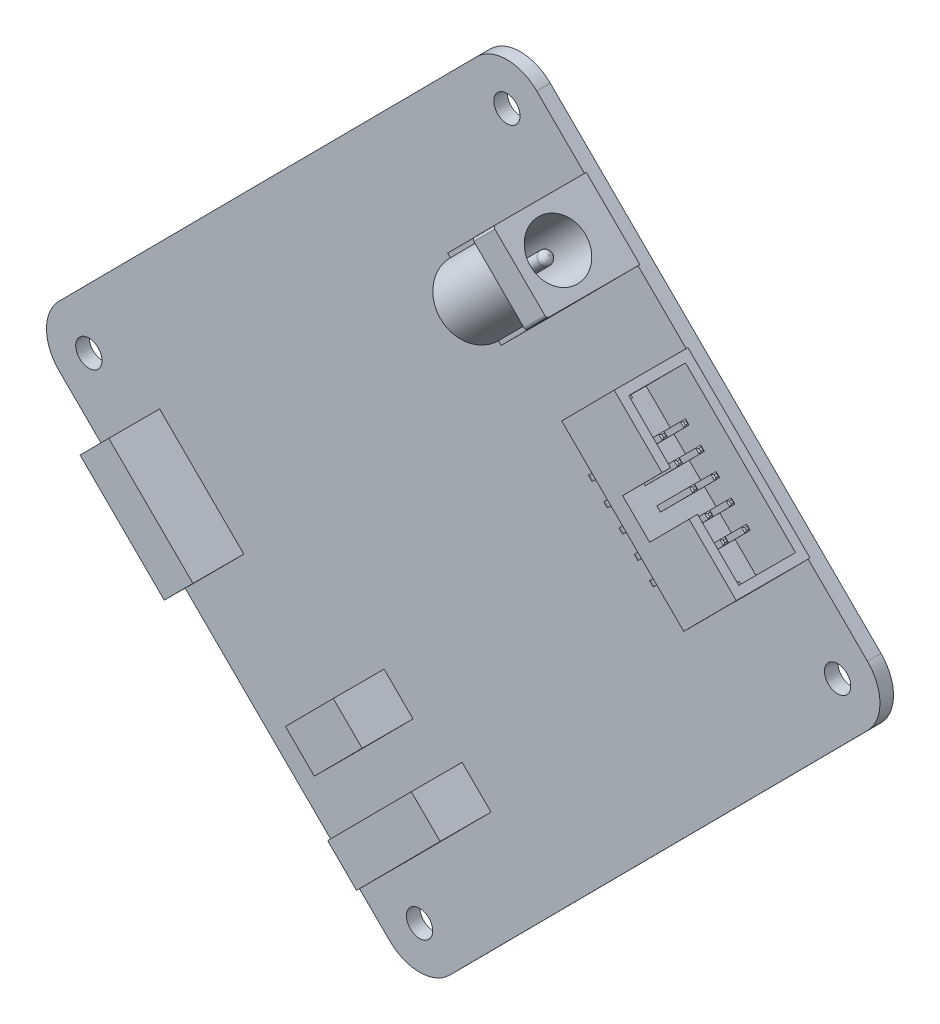
SolidWorks part; units mm, degrees
ref_plane "Front" through (0, 0, 0) normal (0, 0, 1) x (1, 0, 0)
ref_plane "Top" through (0, 0, 0) normal (0, 1, 0) x (1, 0, 0)
ref_plane "Right" through (0, 0, 0) normal (1, 0, 0) x (0, 0, -1)
sketch "草图1" plane through (0, 0, 0) normal (0, 0, 1) x (1, 0, 0)
  line L0 (-46.2191, -2.6231) -> (3.1095, 47.0427)
  line L1 (10.1805, 47.0668) -> (49.2036, 8.3086)
  line L2 (49.2277, 1.2376) -> (-0.1009, -48.4282)
  line L3 (-7.1719, -48.4523) -> (-46.195, -9.6941)
  arc A0 (-0.1009, -48.4282) -> (-7.1719, -48.4523) centre (-3.6484, -44.9047) cw
  arc A1 (49.2036, 8.3086) -> (49.2277, 1.2376) centre (45.6801, 4.761) cw
  arc A2 (3.1095, 47.0427) -> (10.1805, 47.0668) centre (6.657, 43.5192) cw
  arc A3 (-46.2191, -2.6231) -> (-46.195, -9.6941) centre (-42.6716, -6.1466) ccw
  point P6 (-3.6244, -51.9758)
  point P9 (52.7512, 4.7851)
  point P12 (6.6329, 50.5903)
  dimension "D3" = 5
  dimension "D1" = 65
  dimension "D2" = 80
extrude "凸台-拉伸1" add sketch "草图1" along normal blind 1.6
sketch "草图2" plane through (0, 0, 1.6) normal (0, 0, 1) x (1, 0, 0)
  circle A0 centre (6.657, 43.5192) radius 1.55
  circle A1 centre (-42.6716, -6.1466) radius 1.55
  circle A2 centre (-3.6484, -44.9047) radius 1.55
  circle A3 centre (45.6801, 4.761) radius 1.55
  dimension "D1" = 3.1
  dimension "D2" = 3.1
  dimension "D3" = 3.1
  dimension "D4" = 3.1
extrude "切除-拉伸1" cut sketch "草图2" against normal blind 1.6
sketch "草图3" plane through (0, 0, 1.6) normal (0, 0, 1) x (1, 0, 0)
  line L0 (28.0233, 29.768) -> (21.822, 23.5243)
  line L2 (21.822, 23.5243) -> (36.225, 9.219)
  line L3 (36.225, 9.219) -> (42.4263, 15.4627)
  line L4 (42.4263, 15.4627) -> (28.0233, 29.768)
  line L5 (35.2248, 22.6153) -> (29.0235, 16.3716) construction
  line L6 (3.1095, 47.0427) -> (-46.2191, -2.6231) construction
  line L7 (49.2036, 8.3086) -> (10.1805, 47.0668) construction
  dimension "D1" = 8.8
  dimension "D2" = 40
  dimension "D3" = 10.15
  dimension "D4" = 8.5
extrude "凸台-拉伸2" add sketch "草图3" along normal blind 8.7
sketch "草图4" plane through (28.7998, 28.9967, 0) normal (0.7047, 0.7095, 0) x (0.7095, -0.7047, 0)
  line L0 (18.2055, -9.3) -> (11.3555, -9.3)
  line L1 (11.3555, -9.3) -> (11.3555, -10.3)
  line L2 (19.2055, -10.3) -> (-1.0945, -10.3) construction
  line L3 (11.3555, -10.3) -> (6.8555, -10.3)
  line L4 (6.8555, -10.3) -> (6.8555, -9.3)
  line L5 (6.8555, -9.3) -> (-0.0945, -9.3)
  line L6 (-0.0945, -9.3) -> (-0.0945, -2.6)
  line L7 (-0.0945, -2.6) -> (18.2055, -2.6)
  line L8 (18.2055, -2.6) -> (18.2055, -9.3)
  line L9 (-1.0945, -10.3) -> (-1.0945, -1.6) construction
  line L10 (19.2055, -10.3) -> (19.2055, -1.6) construction
  line L11 (29.0555, -1.6) -> (19.2055, -1.6) construction
  dimension "D1" = 1
  dimension "D2" = 1
  dimension "D3" = 1
  dimension "D4" = 1
  dimension "D5" = 1
  dimension "D6" = 4.5
  dimension "D7" = 7.85
extrude "切除-拉伸2" cut sketch "草图4" against normal offset from surface (6.6 mm away) 2.2 up to face at (29.0235, 16.3716, 5.95)
sketch "草图5" plane through (13.6265, -13.534, 0) normal (0.7095, -0.7047, 0) x (0, 0, -1)
  line L0 (-7.8, 32.0686) -> (-7.8, 38.5686)
  line L1 (-10.3, 32.0686) -> (-1.6, 32.0686) construction
  line L2 (-7.8, 38.5686) -> (-4.4, 38.5686)
  line L3 (-4.4, 38.5686) -> (-4.4, 32.0686)
  line L4 (-4.4, 32.0686) -> (-7.8, 32.0686)
  line L5 (-10.3, 32.0686) -> (-10.3, 40.8686) construction
  dimension "D1" = 3.4
  dimension "D2" = 6.5
  dimension "D3" = 2.5
extrude "切除-拉伸3" cut sketch "草图5" against normal blind 1.3
sketch "草图6" plane through (-0.7766, 0.7713, 0) normal (-0.7095, 0.7047, 0) x (0, 0, 1)
  line L0 (10.3, 32.0686) -> (1.6, 32.0686) construction
  line L1 (7.8, 32.0686) -> (4.4, 32.0686)
  line L2 (7.8, 32.0686) -> (7.8, 38.5686)
  line L3 (7.8, 38.5686) -> (4.4, 38.5686)
  line L4 (4.4, 32.0686) -> (4.4, 38.5686)
  line L5 (10.3, 40.8686) -> (10.3, 32.0686) construction
  dimension "D1" = 3.4
  dimension "D2" = 6.5
  dimension "D3" = 2.5
extrude "切除-拉伸4" cut sketch "草图6" against normal blind 1.3
sketch "草图7" plane through (24.1488, 24.3139, 0) normal (0.7047, 0.7095, 0) x (0.7095, -0.7047, 0)
  line L0 (11.3555, -9.3) -> (18.2055, -9.3) construction
  line L1 (14.7055, -7.8) -> (14.1055, -7.8)
  line L2 (14.7055, -7.8) -> (14.7055, -7.2)
  line L3 (14.7055, -7.2) -> (14.1055, -7.2)
  line L4 (14.1055, -7.8) -> (14.1055, -7.2)
  line L5 (18.2055, -9.3) -> (18.2055, -2.6) construction
  line L6 (12.1655, -7.8) -> (12.1655, -7.2)
  line L7 (12.1655, -7.8) -> (11.5655, -7.8)
  line L8 (11.5655, -7.8) -> (11.5655, -7.2)
  line L9 (12.1655, -7.2) -> (11.5655, -7.2)
  line L10 (9.6255, -7.8) -> (9.6255, -7.2)
  line L11 (9.6255, -7.8) -> (9.0255, -7.8)
  line L12 (9.0255, -7.8) -> (9.0255, -7.2)
  line L13 (9.6255, -7.2) -> (9.0255, -7.2)
  line L14 (7.0855, -7.8) -> (7.0855, -7.2)
  line L15 (7.0855, -7.8) -> (6.4855, -7.8)
  line L16 (6.4855, -7.8) -> (6.4855, -7.2)
  line L17 (7.0855, -7.2) -> (6.4855, -7.2)
  line L18 (4.5455, -7.8) -> (4.5455, -7.2)
  line L19 (4.5455, -7.8) -> (3.9455, -7.8)
  line L20 (3.9455, -7.8) -> (3.9455, -7.2)
  line L21 (4.5455, -7.2) -> (3.9455, -7.2)
  line L22 (12.1655, -5.26) -> (12.1655, -4.66)
  line L23 (12.1655, -5.26) -> (11.5655, -5.26)
  line L24 (11.5655, -5.26) -> (11.5655, -4.66)
  line L25 (12.1655, -4.66) -> (11.5655, -4.66)
  line L26 (9.6255, -5.26) -> (9.6255, -4.66)
  line L27 (9.6255, -5.26) -> (9.0255, -5.26)
  line L28 (9.0255, -5.26) -> (9.0255, -4.66)
  line L29 (9.6255, -4.66) -> (9.0255, -4.66)
  line L30 (7.0855, -5.26) -> (7.0855, -4.66)
  line L31 (7.0855, -5.26) -> (6.4855, -5.26)
  line L32 (6.4855, -5.26) -> (6.4855, -4.66)
  line L33 (7.0855, -4.66) -> (6.4855, -4.66)
  line L34 (4.5455, -5.26) -> (4.5455, -4.66)
  line L35 (4.5455, -5.26) -> (3.9455, -5.26)
  line L36 (3.9455, -5.26) -> (3.9455, -4.66)
  line L37 (4.5455, -4.66) -> (3.9455, -4.66)
  line L38 (14.7055, -5.26) -> (14.7055, -4.66)
  line L39 (14.7055, -5.26) -> (14.1055, -5.26)
  line L40 (14.1055, -5.26) -> (14.1055, -4.66)
  line L41 (14.7055, -4.66) -> (14.1055, -4.66)
  point P6 (14.7805, -9.3)
  dimension "D1" = 0.6
  dimension "D2" = 0.6
  dimension "D3" = 1.5
  dimension "D4" = 3.5
  dimension "D5" = 5
  dimension "D6" = 2
extrude "凸台-拉伸3" add sketch "草图7" along normal offset from surface 1 and the other way offset from surface (4.2 mm away) 2 up to face at (35.2366, 22.6036, 7.2333) other way up to face at (29.0235, 16.3716, 6.05)
sketch "草图8" plane through (21.1891, 21.334, 0) normal (-0.7047, -0.7095, 0) x (0.7095, -0.7047, 0)
  line L21 (4.5455, 7.8) -> (3.9455, 7.8) construction
  line L26 (3.9455, 7.8) -> (4.5455, 7.8)
  line L27 (3.9455, 7.8) -> (3.9455, 7.2)
  line L28 (3.9455, 7.2) -> (4.5455, 7.2)
  line L29 (4.5455, 7.8) -> (4.5455, 7.2)
  line L30 (7.0855, 7.8) -> (6.4855, 7.8) construction
  line L31 (6.4855, 7.8) -> (7.0855, 7.8)
  line L32 (6.4855, 7.8) -> (6.4855, 7.2)
  line L33 (6.4855, 7.2) -> (7.0855, 7.2)
  line L34 (7.0855, 7.8) -> (7.0855, 7.2)
  line L35 (6.4855, 7.8) -> (6.4855, 7.2) construction
  line L36 (6.4855, 7.2) -> (7.0855, 7.2) construction
  line L37 (9.6255, 7.8) -> (9.0255, 7.8) construction
  line L38 (9.0255, 7.8) -> (9.6255, 7.8)
  line L39 (9.0255, 7.8) -> (9.0255, 7.2)
  line L40 (9.0255, 7.2) -> (9.6255, 7.2)
  line L41 (9.6255, 7.8) -> (9.6255, 7.2)
  line L42 (9.0255, 7.8) -> (9.0255, 7.2) construction
  line L43 (9.0255, 7.2) -> (9.6255, 7.2) construction
  line L44 (12.1655, 7.8) -> (11.5655, 7.8) construction
  line L45 (11.5655, 7.8) -> (12.1655, 7.8)
  line L46 (11.5655, 7.8) -> (11.5655, 7.2)
  line L47 (11.5655, 7.2) -> (12.1655, 7.2)
  line L48 (12.1655, 7.8) -> (12.1655, 7.2)
  line L49 (11.5655, 7.2) -> (12.1655, 7.2) construction
  line L50 (14.7055, 7.8) -> (14.1055, 7.8) construction
  line L51 (14.1055, 7.8) -> (14.7055, 7.8)
  line L52 (14.1055, 7.8) -> (14.1055, 7.2)
  line L53 (14.1055, 7.2) -> (14.7055, 7.2)
  line L54 (14.7055, 7.8) -> (14.7055, 7.2)
  line L55 (14.1055, 7.2) -> (14.7055, 7.2) construction
extrude "凸台-拉伸4" add sketch "草图8" along normal blind 2.54
sketch "草图9" plane through (0, 0, 4.66) normal (0, 0, -1) x (-1, 0, 0)
  line L0 (-31.6228, 10.9711) -> (-31.1971, 11.3939)
  line L1 (-31.1971, 11.3939) -> (-31.6228, 10.9711) construction
  line L2 (-33.0322, 12.3901) -> (-31.6228, 10.9711) construction
  line L3 (-32.6065, 12.8129) -> (-29.4072, 9.5918) construction
  line L4 (-31.1971, 11.3939) -> (-31.6228, 11.8225)
  line L5 (-32.6065, 12.8129) -> (-31.1971, 11.3939) construction
  line L6 (-31.6228, 11.8225) -> (-32.0486, 11.3997)
  line L7 (-32.0486, 11.3997) -> (-31.6228, 10.9711)
  line L8 (-29.8207, 12.761) -> (-29.395, 13.1838)
  line L9 (-29.395, 13.1838) -> (-29.8207, 12.761) construction
  line L10 (-31.2301, 14.18) -> (-29.8207, 12.761) construction
  line L11 (-29.395, 13.1838) -> (-29.8207, 13.6125)
  line L12 (-30.8044, 14.6029) -> (-29.395, 13.1838) construction
  line L13 (-29.8207, 13.6125) -> (-30.2464, 13.1896)
  line L14 (-30.2464, 13.1896) -> (-29.8207, 12.761)
  line L15 (-28.0185, 14.5509) -> (-27.5928, 14.9738)
  line L16 (-29.4279, 15.97) -> (-28.0185, 14.5509) construction
  line L17 (-29.0022, 16.3928) -> (-27.5928, 14.9738) construction
  line L18 (-27.5928, 14.9738) -> (-28.0185, 14.5509) construction
  line L19 (-27.5928, 14.9738) -> (-28.0185, 15.4024)
  line L20 (-28.0185, 15.4024) -> (-28.4442, 14.9796)
  line L21 (-28.4442, 14.9796) -> (-28.0185, 14.5509)
  line L22 (-26.2164, 16.3409) -> (-25.7907, 16.7637)
  line L23 (-27.6258, 17.7599) -> (-26.2164, 16.3409) construction
  line L24 (-25.7907, 16.7637) -> (-26.2164, 16.3409) construction
  line L25 (-27.2001, 18.1827) -> (-25.7907, 16.7637) construction
  line L26 (-25.7907, 16.7637) -> (-26.2164, 17.1923)
  line L27 (-26.2164, 17.1923) -> (-26.6421, 16.7695)
  line L28 (-26.6421, 16.7695) -> (-26.2164, 16.3409)
  line L29 (-24.4142, 18.1308) -> (-23.9885, 18.5536)
  line L30 (-25.8236, 19.5498) -> (-24.4142, 18.1308) construction
  line L31 (-23.9885, 18.5536) -> (-24.4142, 18.1308) construction
  line L32 (-23.9885, 18.5536) -> (-24.4142, 18.9822)
  line L33 (-25.3979, 19.9726) -> (-23.9885, 18.5536) construction
  line L34 (-24.4142, 18.9822) -> (-24.8399, 18.5594)
  line L35 (-24.8399, 18.5594) -> (-24.4142, 18.1308)
extrude "凸台-拉伸5" add sketch "草图9" along normal up to surface (3.06 mm away) up to face at (47.2301, 4.761, 1.6)
sketch "草图10" plane through (0, 0, 7.2) normal (0, 0, -1) x (-1, 0, 0)
  line L0 (-29.8329, 9.1689) -> (-29.4072, 9.5918)
  line L1 (-27.6051, 11.3817) -> (-28.0308, 10.9589) construction
  line L2 (-33.0322, 12.3901) -> (-29.8329, 9.1689) construction
  line L3 (-32.6065, 12.8129) -> (-29.4072, 9.5918) construction
  line L4 (-29.4072, 9.5918) -> (-29.8329, 10.0204)
  line L5 (-29.8329, 10.0204) -> (-30.2586, 9.5976)
  line L6 (-30.2586, 9.5976) -> (-29.8329, 9.1689)
  line L7 (-28.0308, 10.9589) -> (-27.6051, 11.3817)
  line L8 (-31.2301, 14.18) -> (-28.0308, 10.9589) construction
  line L10 (-27.6051, 11.3817) -> (-28.0308, 11.8103)
  line L11 (-30.8044, 14.6029) -> (-27.6051, 11.3817) construction
  line L12 (-28.0308, 11.8103) -> (-28.4565, 11.3875)
  line L13 (-28.4565, 11.3875) -> (-28.0308, 10.9589)
  line L14 (-26.2286, 12.7488) -> (-25.8029, 13.1716)
  line L16 (-29.4279, 15.97) -> (-26.2286, 12.7488) construction
  line L17 (-25.8029, 13.1716) -> (-26.2286, 13.6002)
  line L18 (-29.0022, 16.3928) -> (-25.8029, 13.1716) construction
  line L19 (-26.2286, 13.6002) -> (-26.6543, 13.1774)
  line L20 (-26.6543, 13.1774) -> (-26.2286, 12.7488)
  line L21 (-24.4264, 14.5387) -> (-24.0007, 14.9615)
  line L22 (-27.6258, 17.7599) -> (-24.4264, 14.5387) construction
  line L24 (-24.0007, 14.9615) -> (-24.4264, 15.3901)
  line L25 (-27.2001, 18.1827) -> (-24.0007, 14.9615) construction
  line L26 (-24.4264, 15.3901) -> (-24.8522, 14.9673)
  line L27 (-24.8522, 14.9673) -> (-24.4264, 14.5387)
  line L28 (-22.6243, 16.3286) -> (-22.1986, 16.7514)
  line L29 (-25.8236, 19.5498) -> (-22.6243, 16.3286) construction
  line L30 (-22.1986, 16.7514) -> (-22.6243, 16.3286) construction
  line L31 (-25.3979, 19.9726) -> (-22.1986, 16.7514) construction
  line L32 (-22.1986, 16.7514) -> (-22.6243, 17.1801)
  line L33 (-22.6243, 17.1801) -> (-23.05, 16.7572)
  line L34 (-23.05, 16.7572) -> (-22.6243, 16.3286)
extrude "凸台-拉伸6" add sketch "草图10" along normal up to surface (5.6 mm away) up to face at (26.2164, 16.7666, 1.6)
fillet "圆角2" radius 0.6 10 edges at (24.2014, 18.3422, 5.26) (26.0035, 16.5523, 5.26) (27.8057, 14.7624, 5.26) (29.6078, 12.9724, 5.26) (31.41, 11.1825, 5.26) (22.4114, 16.54, 7.8) (27.8179, 11.1703, 7.8) (29.6201, 9.3803, 7.8) (26.0158, 12.9602, 7.8) (24.2136, 14.7501, 7.8)
chamfer "倒角1" distance 0.15 angle 45 40 edges at (38.316, 18.1357, 5.26) (38.1031, 18.3471, 4.96) (38.316, 18.1357, 4.66) (38.5288, 17.9243, 4.96) (36.5138, 19.9256, 5.26) (36.301, 20.137, 4.96) (36.5138, 19.9256, 4.66) (36.7267, 19.7142, 4.96) (34.7117, 21.7156, 5.26) (34.4988, 21.927, 4.96) (34.7117, 21.7156, 4.66) (34.9245, 21.5042, 4.96) (32.9095, 23.5055, 5.26) (32.6967, 23.7169, 4.96) (32.9095, 23.5055, 4.66) (33.1224, 23.2941, 4.96) (31.1074, 25.2954, 5.26) (30.8945, 25.5068, 4.96) (31.1074, 25.2954, 4.66) (31.3202, 25.084, 4.96) (31.1074, 25.2954, 7.8) (30.8945, 25.5068, 7.5) (31.1074, 25.2954, 7.2) (31.3202, 25.084, 7.5) (32.9095, 23.5055, 7.8) (32.6967, 23.7169, 7.5) (32.9095, 23.5055, 7.2) (33.1224, 23.2941, 7.5) (34.7117, 21.7156, 7.8) (34.4988, 21.927, 7.5) (34.7117, 21.7156, 7.2) (34.9245, 21.5042, 7.5) (36.5138, 19.9256, 7.8) (36.301, 20.137, 7.5) (36.5138, 19.9256, 7.2) (36.7267, 19.7142, 7.5) (38.5288, 17.9243, 7.5) (38.316, 18.1357, 7.8) (38.1031, 18.3471, 7.5) (38.316, 18.1357, 7.2)
sketch "草图12" plane through (0, 0, 1.6) normal (0, 0, 1) x (1, 0, 0)
  line L0 (-34.3224, -7.6738) -> (-24.3893, -17.5395)
  line L1 (-24.3893, -17.5395) -> (-27.7718, -20.9451)
  line L2 (-27.7718, -20.9451) -> (-37.705, -11.0794)
  line L3 (-37.705, -11.0794) -> (-34.3224, -7.6738)
  line L5 (-46.195, -9.6941) -> (-7.1719, -48.4523) construction
  line L6 (3.1095, 47.0427) -> (-46.2191, -2.6231) construction
  dimension "D1" = 14
  dimension "D2" = 4.8
  dimension "D3" = 5
  dimension "D4" = 12
extrude "凸台-拉伸7" add sketch "草图12" along normal blind 6
sketch "草图13" plane through (0, 0, 1.6) normal (0, 0, 1) x (1, 0, 0)
  line L0 (-5.0819, -39.2527) -> (4.7838, -29.3196)
  line L1 (4.7838, -29.3196) -> (1.3781, -25.937)
  line L2 (1.3781, -25.937) -> (-8.4876, -35.8702)
  line L3 (-8.4876, -35.8702) -> (-5.0819, -39.2527)
  line L5 (-0.1009, -48.4282) -> (49.2277, 1.2376) construction
  line L6 (-46.195, -9.6941) -> (-7.1719, -48.4523) construction
  line L7 (-7.831, -21.0186) -> (-13.4686, -26.6947)
  line L8 (-13.4686, -26.6947) -> (-10.0629, -30.0773)
  line L9 (-10.0629, -30.0773) -> (-4.4254, -24.4012)
  line L10 (-4.4254, -24.4012) -> (-7.831, -21.0186)
  dimension "D1" = 14
  dimension "D2" = 4.8
  dimension "D3" = 10
  dimension "D4" = 8
  dimension "D5" = 8
  dimension "D6" = 4.8
  dimension "D7" = 20
  dimension "D8" = 11
extrude "凸台-拉伸8" add sketch "草图13" along normal blind 6
sketch "草图14" plane through (0, 0, 1.6) normal (0, 0, 1) x (1, 0, 0)
  line L0 (22.3472, 35.4055) -> (12.4815, 25.4724)
  line L1 (12.4815, 25.4724) -> (6.1668, 31.7442)
  line L2 (6.1668, 31.7442) -> (16.0325, 41.6773)
  line L3 (16.0325, 41.6773) -> (22.3472, 35.4055)
  line L4 (33.6639, 24.1657) -> (28.0233, 29.768) construction
  line L5 (28.0233, 29.768) -> (21.822, 23.5243) construction
  dimension "D1" = 8.9
  dimension "D2" = 14
  dimension "D3" = 8
extrude "凸台-拉伸9" add sketch "草图14" along normal blind 11
sketch "草图15" plane through (18.9341, 19.0635, 0) normal (-0.7047, -0.7095, 0) x (0.7095, -0.7047, 0)
  line L0 (-25.9445, 1.6) -> (29.0555, 1.6) construction
  line L1 (-17.5445, 8.1) -> (-19.3128, 8.1)
  line L2 (-19.3128, 8.1) -> (-19.3128, 13.5514)
  line L3 (-19.3128, 13.5514) -> (-8.259, 13.5514)
  line L4 (-8.259, 13.5514) -> (-8.259, 8.1)
  line L5 (-8.259, 8.1) -> (-9.5445, 8.1)
  arc A0 (-9.5445, 8.1) -> (-17.5445, 8.1) centre (-13.5445, 8.1) ccw
  dimension "D1" = 8
  dimension "D2" = 6.5
extrude "切除-拉伸5" cut sketch "草图15" against normal offset from surface (10.5 mm away) 3.5 up to face at (19.1898, 38.5414, 7.1)
fillet "圆角3" radius 0.3 2 edges at (21.114, 34.1639, 12.6) (14.7993, 40.4357, 12.6)
sketch "草图16" plane through (28.7998, 28.9967, 0) normal (0.7047, 0.7095, 0) x (0.7095, -0.7047, 0)
  line L0 (-9.0945, -1.6) -> (-17.9945, -1.6) construction
  circle A0 centre (-13.5445, -8.1) radius 3.25
  dimension "D1" = 6.5
  dimension "D2" = 6.5
extrude "切除-拉伸6" cut sketch "草图16" against normal blind 11.5
sketch "草图17" plane through (20.6958, 20.8373, 0) normal (0.7047, 0.7095, 0) x (0.7095, -0.7047, 0)
  circle A0 centre (-13.5445, -8.1) radius 0.75
  dimension "D1" = 1.5
extrude "凸台-拉伸10" add sketch "草图17" along normal blind 10
fillet "圆角4" radius 0.7 1 edges at (17.6007, 38.0057, 8.1)
